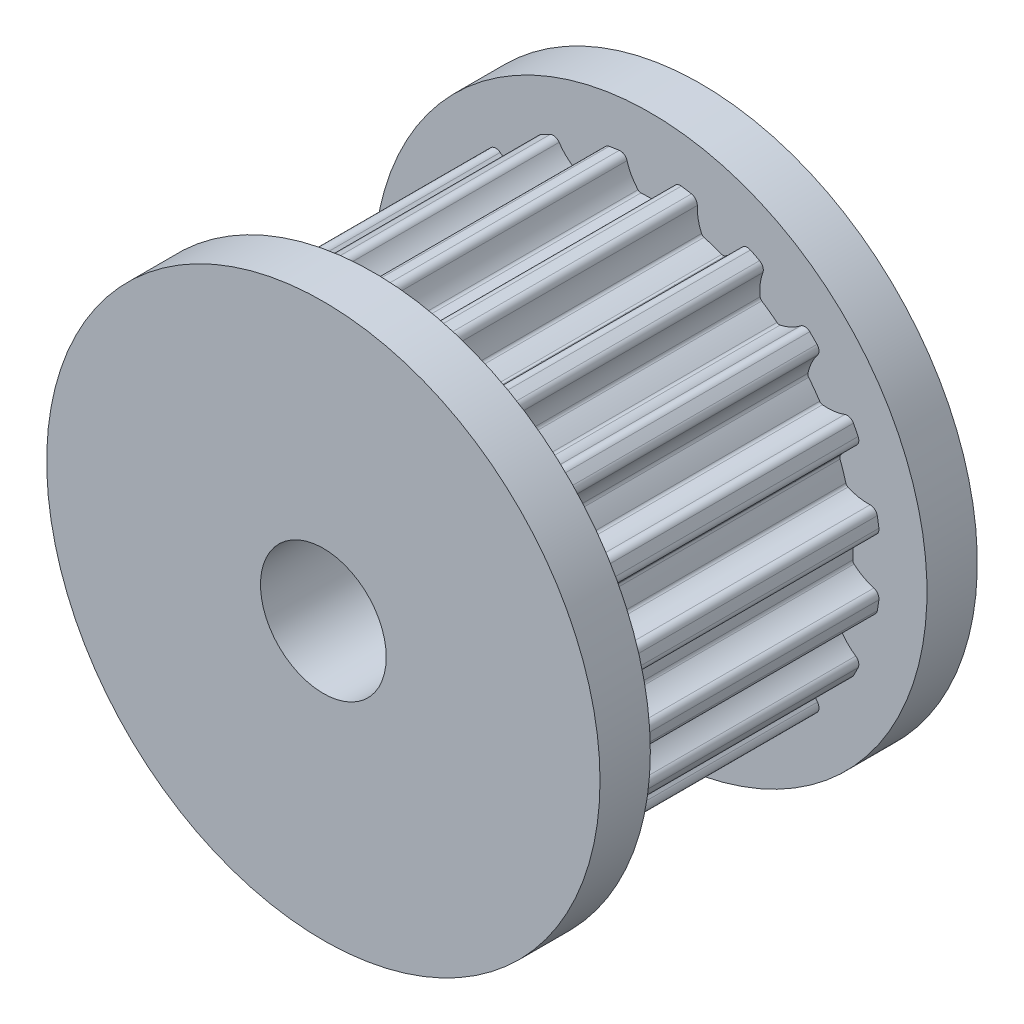
SolidWorks part; units mm, degrees
material "6061-T6 (SS)"
ref_plane "前基準面" through (0, 0, 0) normal (0, 0, 1) x (1, 0, 0)
ref_plane "上基準面" through (0, 0, 0) normal (0, 1, 0) x (1, 0, 0)
ref_plane "右基準面" through (0, 0, 0) normal (1, 0, 0) x (0, 0, -1)
sketch "草圖1" plane through (0, 0, 0) normal (0, 0, 1) x (1, 0, 0)
  circle A0 centre (0, 0) radius 9.17
  dimension "D1" = 18.34
extrude "填料-伸長1" add sketch "草圖1" along normal mid plane 11
sketch "草圖2" plane through (0, 0, 5.5) normal (0, 0, 1) x (1, 0, 0)
  line L0 (0, 0) -> (0, 9.17) construction
  line L1 (0, 9.17) -> (0, 9.424) construction
  line L2 (-0.975, 9.424) -> (0.975, 9.424) construction
  circle A0 centre (0, 0) radius 9.17 construction
  arc A1 (-0.3728, 8.0514) -> (0.3728, 8.0514) centre (0, 0) cw
  arc A2 (-0.3728, 8.0514) -> (-0.4911, 8.1007) centre (-0.3798, 8.2012) cw
  arc A3 (-0.4911, 8.1007) -> (-0.9252, 8.8857) centre (0.975, 9.424) cw
  arc A4 (-1.2322, 9.0868) -> (-0.9252, 8.8857) centre (-1.1946, 8.8094) cw
  arc A5 (0.3728, 8.0514) -> (0.4911, 8.1007) centre (0.3798, 8.2012) ccw
  arc A6 (0.4911, 8.1007) -> (0.9252, 8.8857) centre (-0.975, 9.424) ccw
  arc A7 (1.2322, 9.0868) -> (0.9252, 8.8857) centre (1.1946, 8.8094) ccw
  arc A8 (-1.2322, 9.0868) -> (1.2322, 9.0868) centre (0, 0) cw
  dimension "D1" = 0.15
  dimension "D2" = 1.975
  dimension "D3" = 0.28
  dimension "D4" = 1.11
  dimension "D5" = 0.254
  dimension "D6" = 1.95
extrude "除料-伸長1" cut sketch "草圖2" against normal through all and the other way through all
pattern_circular "環狀複製排列1" count 20 over 360 about axis through (0, 0, 0) along (0, 0, 1) of "除料-伸長1"
sketch "草圖3" plane through (0, 0, 5.5) normal (0, 0, 1) x (1, 0, 0)
  circle A0 centre (0, 0) radius 11
  dimension "D1" = 22
extrude "填料-伸長2" add sketch "草圖3" along normal blind 2
sketch "草圖9" plane through (0, 0, -5.5) normal (0, 0, -1) x (-1, 0, 0)
  circle A0 centre (0, 0) radius 11
  circle A1 centre (0, 0) radius 11 construction
extrude "填料-伸長3" add sketch "草圖9" along normal blind 2
sketch "草圖4" plane through (0, 0, 7.5) normal (0, 0, 1) x (1, 0, 0)
  circle A0 centre (0, 0) radius 2.5
  dimension "D1" = 5
extrude "除料-伸長2" cut sketch "草圖4" against normal through all
sketch "草圖10" plane through (0, 0, 0) normal (0, 1, 0) x (1, 0, 0)
  circle A0 centre (0, 0) radius 2
  dimension "D1" = 4
extrude "除料-伸長3" cut sketch "草圖10" against normal through all
sketch "草圖11" plane through (0, 0, 0) normal (1, 0, 0) x (0, 0, -1)
  circle A0 centre (0, 0) radius 2
  dimension "D1" = 4
extrude "除料-伸長4" cut sketch "草圖11" against normal through all
